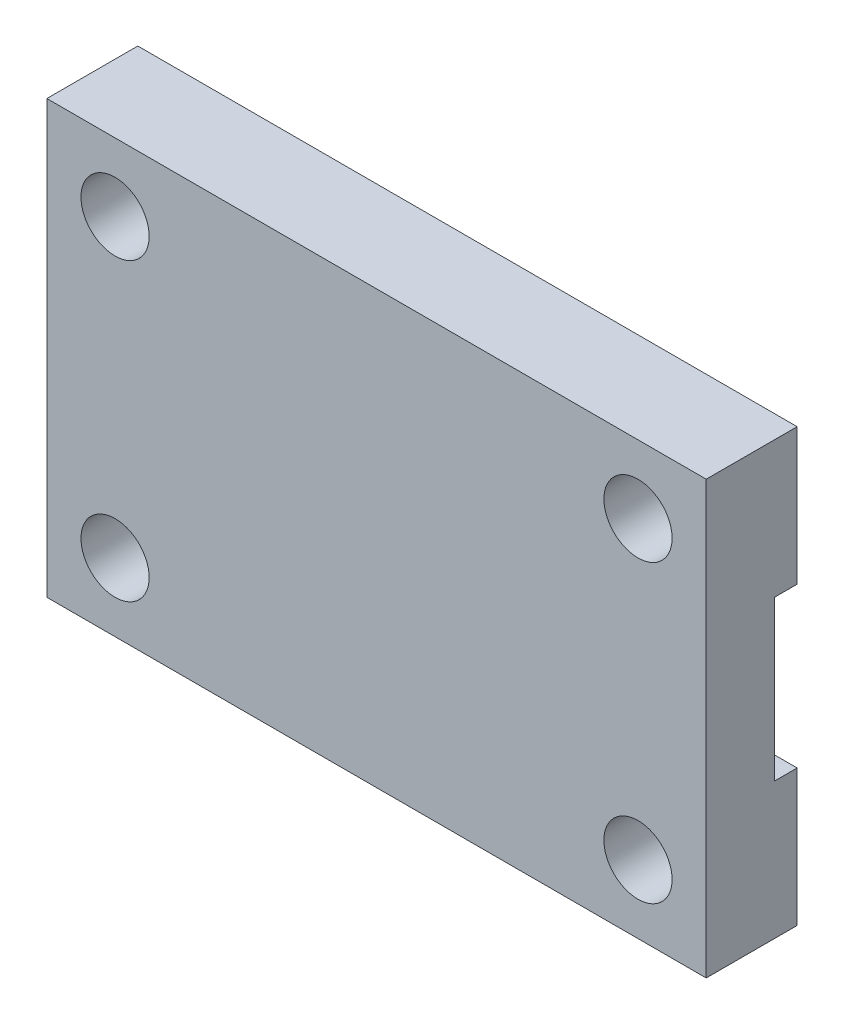
SolidWorks part; units mm, degrees
ref_plane "Front Plane" through (0, 0, 0) normal (0, 0, 1) x (1, 0, 0)
ref_plane "Top Plane" through (0, 0, 0) normal (0, 1, 0) x (1, 0, 0)
ref_plane "Right Plane" through (0, 0, 0) normal (1, 0, 0) x (0, 0, -1)
sketch "Sketch1" plane through (0, 0, 0) normal (0, 0, 1) x (1, 0, 0)
  line L0 (0, 0) -> (29, 0)
  line L1 (29, 0) -> (29, 19)
  line L2 (29, 19) -> (0, 19)
  line L3 (0, 19) -> (0, 0)
  line L4 (0, 19) -> (6, 13) construction
  line L5 (6, 13) -> (0, 13) construction
  line L6 (6, 13) -> (6, 19) construction
  line L7 (29, 0) -> (23, 6) construction
  line L8 (23, 6) -> (29, 6) construction
  line L9 (23, 6) -> (23, 0) construction
  line L10 (3, 16) -> (26, 16) construction
  line L11 (26, 16) -> (26, 3) construction
  line L12 (26, 3) -> (3, 3) construction
  line L13 (3, 3) -> (3, 16) construction
  circle A0 centre (3, 16) radius 1.5
  circle A1 centre (3, 3) radius 1.5
  circle A2 centre (26, 3) radius 1.5
  circle A3 centre (26, 16) radius 1.5
  dimension "D4" = 3
  dimension "D1" = 29
  dimension "D2" = 19
  dimension "D3" = 6
extrude "Boss-Extrude1" add sketch "Sketch1" along normal blind 4
sketch "Sketch2" plane through (0, 0, 0) normal (0, 0, -1) x (-1, 0, 0)
  line L0 (-29, 19) -> (-29, 13) construction
  line L1 (-29, 0) -> (-29, 19) construction
  line L2 (-29, 0) -> (-29, 6) construction
  line L3 (-29, 13) -> (-29, 6)
  line L4 (-29, 6) -> (0, 6)
  line L5 (0, 19) -> (0, 0) construction
  line L6 (0, 6) -> (0, 13)
  line L7 (0, 13) -> (-29, 13)
  dimension "D1" = 7
extrude "Cut-Extrude1" cut sketch "Sketch2" against normal blind 1
equation "\"board_length\"= 260mm"
equation "\"board_height\"= 200mm"
equation "\"board_width\"= 16.5mm"
equation "\"token_thickness\"= 7mm"
equation "\"token_diameter\"= 32mm"
equation "\"board_side_lower_height\"= 55mm"
equation "\"board_side_height\"= 156.5mm"
equation "\"board_side_length\"= 100mm"
equation "\"board_slot_width\"= \"board_length\" / 7"
equation "\"token_ridge\"= ( \"token_thickness\" - 4mm ) / 2"
equation "\"token_ridge_width\"= 1.5mm"
equation "\"25T_outer_diameter\"= 20mm"
equation "\"25T_inner_diameter\"= 9mm"
equation "\"2T_screw_distance\"= 14mm"
equation "\"2T_outer_thickness\"= 2mm"
equation "\"2T_inner_thickness\"= 4.5mm"
equation "\"MG996R_outer_length\"= 54mm"
equation "\"MG996R_inner_length\"= 40mm"
equation "\"MG996R_width\"= 20mm"
equation "\"MG996R_height\"= 26.6mm"
equation "\"MG996R_full_height\"= 45.7mm"
equation "\"MG996R_full_width\"= 55.5mm"
equation "\"MG996R_screw_distance\"= 10mm"
equation "\"magnet_diameter\"= 10mm"
equation "\"magnet_thickness\"= 2mm"
equation "\"dispenser_barrel_margin\"= 2.5mm"
equation "\"dispenser_wheel_width\"= \"token_thickness\" + 5mm"
equation "\"dispenser_cover_margin\"= 3.0mm"
equation "\"dispenser_cover_thickness\"= 5.0mm"
equation "\"MG996R_major_axis_distance\"= 34.3mm"
equation "\"MG996R_major_screw_distance\"= 48.6mm"
equation "\"MG996R_minor_screw_distance\"= 9.9mm"
equation "\"MG996R_mid_height\"= 37.5mm"
equation "\"dispenser_slope\"= 30deg"
equation "\"dispenser_cover_length\"= 16mm"
equation "\"dispenser_carrier_width\"= 3.5mm"
equation "\"dispenser_carrier_height\"= 40mm"
equation "\"carrier_width\"= \"shaft_diameter\" * 2"
equation "\"shaft_diameter\"= 8mm"
equation "\"carrier_thickness\"=16"
equation "\"GT2_width\"= 7mm"
equation "\"GT2_outer_diameter\"= 18mm"
equation "\"GT2_inner_diameter\"= 12mm"
equation "\"GT2_pitch_diameter\"= 2mm"
equation "\"GT2_tooth_height\"= 1.6mm"
equation "\"GT2_upper_length\"= 0.4mm"
equation "\"belt_holder_width\"= \"GT2_width\" + 2 * 6mm"
equation "\"D1@Sketch1\"=\"dispenser_cover_thickness\"+6mm*4"
equation "\"D2@Sketch1\"=\"belt_holder_width\""
equation "\"D1@Boss-Extrude1\"=\"GT2_pitch_diameter\"*2"
equation "\"D1@Sketch2\"=\"GT2_width\""
equation "\"D1@Cut-Extrude1\"=\"GT2_pitch_diameter\"/2"
